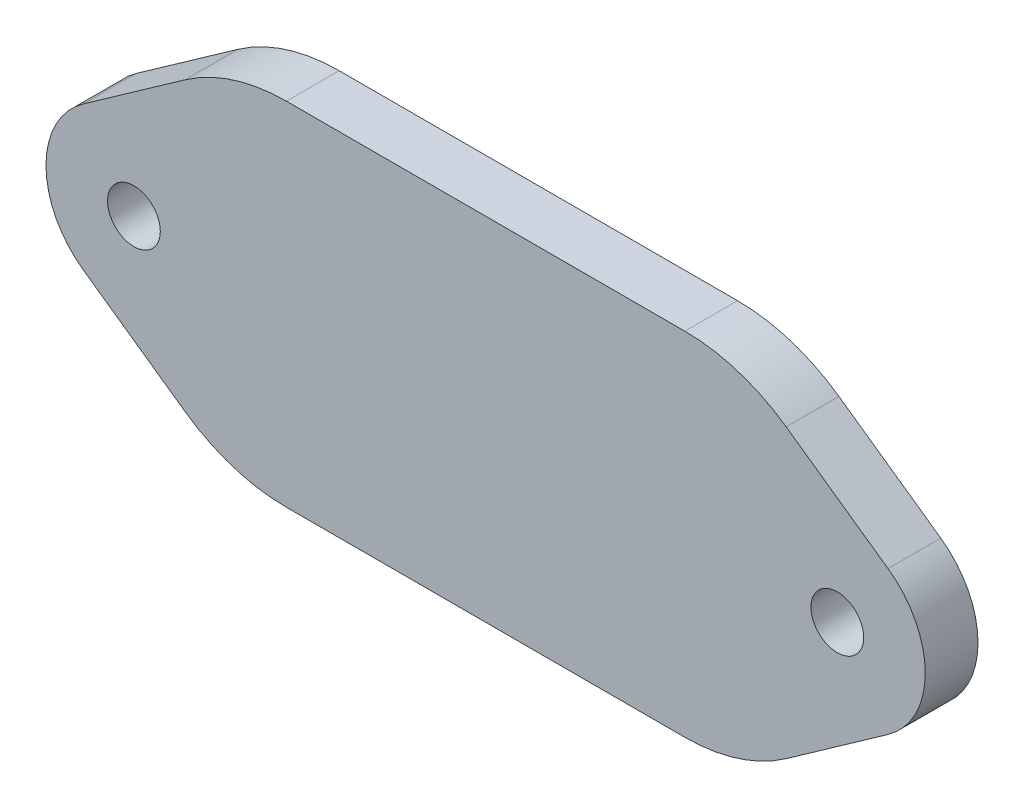
SolidWorks part; units mm, degrees
material "MDF"
ref_plane "Plano frontal" through (0, 0, 0) normal (0, 0, 1) x (1, 0, 0)
ref_plane "Plano superior" through (0, 0, 0) normal (0, 1, 0) x (1, 0, 0)
ref_plane "Plano direito" through (0, 0, 0) normal (1, 0, 0) x (0, 0, -1)
sketch "Esboço1" plane through (0, 0, 0) normal (0, 0, 1) x (1, 0, 0)
  line L0 (-22.8826, 4.0854) -> (-14.5, 10)
  line L1 (-14.5, -10) -> (14.5, -10)
  line L2 (-14.5, -10) -> (-14.5, 10)
  line L3 (-14.5, 10) -> (14.5, 10)
  line L4 (14.5, -10) -> (14.5, 10)
  line L5 (0, 10) -> (0, -10) construction
  line L6 (-14.5, 0) -> (14.5, 0) construction
  line L7 (-22.8826, -4.0854) -> (-14.5, -10)
  line L8 (22.8826, -4.0854) -> (14.5, -10)
  line L9 (22.8826, 4.0854) -> (14.5, 10)
  circle A0 centre (-20, 0) radius 1.5
  circle A1 centre (20, 0) radius 1.5
  arc A2 (-22.8826, 4.0854) -> (-22.8826, -4.0854) centre (-20, 0) ccw
  arc A3 (22.8826, 4.0854) -> (22.8826, -4.0854) centre (20, 0) cw
  point P0 (0, 0)
  dimension "D1" = 3
  dimension "D2" = 40
  dimension "D3" = 5
  dimension "D4" = 20
  dimension "D5" = 29
extrude "Ressalto-extrusão1" add sketch "Esboço1" along normal blind 3 contours L0 A2 L7 L2 A0 | L1 L4 L3 L2 | A3 L9 L4 L8 A1
fillet "Filete1" radius 10 4 edges at (14.5, -10, 1.5) (-14.5, -10, 1.5) (-14.5, 10, 1.5) (14.5, 10, 1.5)
